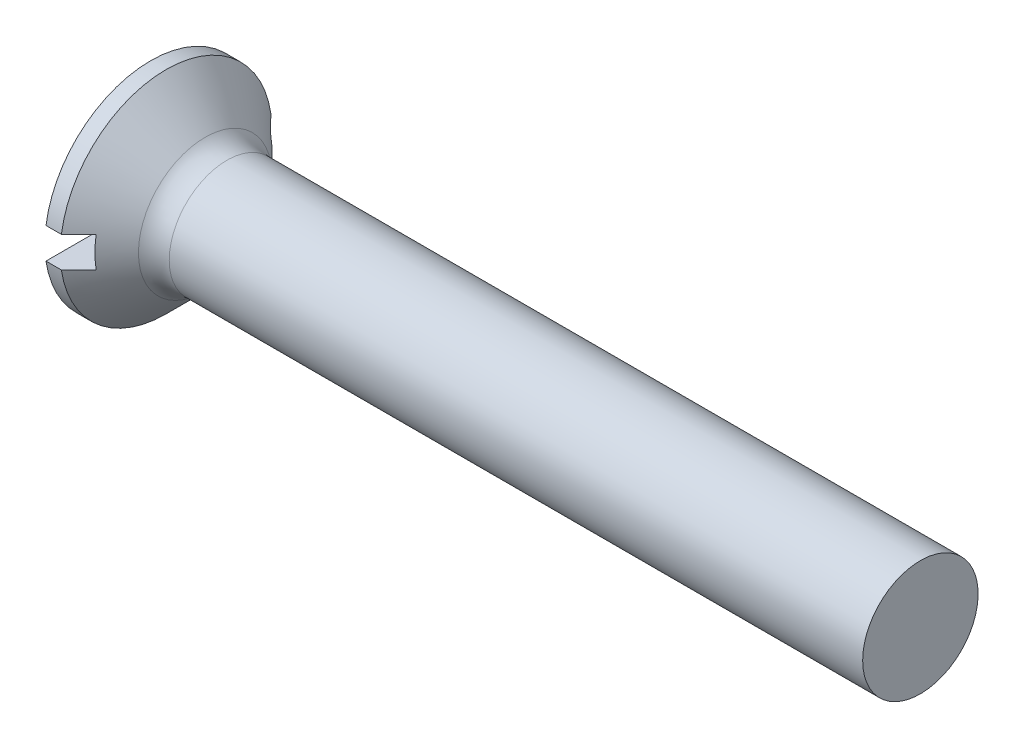
SolidWorks part; units mm, degrees
revolve "Base-Revolve" add sketch "BodySke" angle 360 about L5
sketch "BodySke" plane through (0, 0, 0) normal (0, 0, 1) x (1, 0, 0)
  line L0 (0, 0) -> (0, 2.75)
  line L1 (0, 2.75) -> (0.4, 2.75)
  line L2 (1.65, 1.5) -> (20, 1.5)
  line L3 (20, 1.5) -> (20, 0)
  line L4 (20, 0) -> (0, 0)
  line L5 (-6.35, 0) -> (82.55, 0) construction
  line L6 (1.65, -1.5) -> (20, -1.5) construction
  line L7 (0.4, -2.75) -> (1.65, -1.5) construction
  line L8 (0.4, 2.75) -> (1.65, 1.5)
  line L9 (0, -2.75) -> (0.4, -2.75) construction
  line L10 (2.15, 3.0875) -> (2.15, -6.4375) construction
  line L11 (0, 6.35) -> (0, -3.175) construction
  dimension "Diameter" = 3
  dimension "Length" = 20
  dimension "Head_ht" = 1.65
  dimension "Head_dia" = 5.5
  dimension "Head_ang" = 90
  dimension "D6" = 0.4
  dimension "Advance" = 0.5
  dimension "Thread_nom" = 20
cosmetic thread "ThreadCosmetic" [suppressed] parameters "Thread_length"=17.85, "Thread_minor"=2.439
extrude "Slot" cut sketch "Sketch2" against normal blind 0.85
sketch "Sketch2" plane through (0, 0, 0) normal (-1, 0, 0) x (0, 0, 1)
  line L0 (-2.75, -0.4) -> (2.75, -0.4)
  line L1 (-2.75, -0.4) -> (-2.75, 0.4)
  line L2 (2.75, 0.4) -> (-2.75, 0.4)
  line L3 (2.75, 0.4) -> (2.75, -0.4)
  dimension "Slot_width" = 0.8
  dimension "D1" = 0.4
  dimension "D2" = 5.5
  dimension "D3" = 2.75
ref_plane "Plane1" through (0, 0, 0) normal (0, 0, 1) x (1, 0, 0)
ref_plane "Plane2" through (0, 0, 0) normal (0, 1, 0) x (1, 0, 0)
ref_plane "Plane3" through (0, 0, 0) normal (1, 0, 0) x (0, 0, -1)
fillet "Fillet1" radius 0.8 1 edges at (1.65, 0, 1.5)
sketch "ThdSchSke" plane through (0, 0, 0) normal (0, 0, 1) x (1, 0, 0)
  line L0 (2.15, -1.2195) -> (1.9536, -1.5)
  line L1 (2.15, -1.2195) -> (2.3464, -1.5)
  line L2 (2.3464, -1.5) -> (2.3464, -1.875)
  line L3 (-3.175, 0) -> (5.1513, 0) construction
  line L5 (2.3464, -1.875) -> (1.9536, -1.875)
  line L6 (1.9536, -1.875) -> (1.9536, -1.5)
  line L7 (0, 2.75) -> (0, 0.4) construction
  dimension "Diameter" = 3
  dimension "Thread_minor" = 2.439
  dimension "Start" = 2.15
revolve "ThreadSchematic" [suppressed] cut sketch "ThdSchSke" angle 360 about L3
pattern_linear "ThdSchPat" [suppressed]
equation "\"D1@Sketch2\" = \"Slot_width@Sketch2\" / 2"
equation "\"D2@Sketch2\" = \"Head_dia@BodySke\""
equation "\"D3@Sketch2\" = \"D2@Sketch2\" / 2"
equation "\"Thread_length@ThreadCosmetic\" = ((sgn( (\"Length@BodySke\" - \"Advance@BodySke\" * 1.0 - \"Head_ht@BodySke\" ) - \"Thread_nom@BodySke\" )-1)*( (\"Length@BodySke\" - \"Advance@BodySke\" * 1.0 - \"Head_ht@BodySke\" ) - \"Thread_nom@BodySke\" ))/-2+ \"Thread_nom@BodySke\""
equation "\"Thread_minor@ThdSchSke\" = \"Thread_minor@ThreadCosmetic\""
equation "\"Diameter@ThdSchSke\" = \"Diameter@BodySke\""
equation "\"Overcut@ThdSchSke\" = \"Diameter@BodySke\" * 1.25"
equation "\"Start@ThdSchSke\" = 0.000001 + \"Length@BodySke\" - \"Thread_length@ThreadCosmetic\"  '---Countersunk---"
equation "\"Num_threads@ThdSchPat\" = int( \"Thread_length@ThreadCosmetic\" / \"Advance@BodySke\" + 0.999 )  + 1"
equation "\"Advance@ThdSchPat\" = \"Thread_length@ThreadCosmetic\" /  (\"Num_threads@ThdSchPat\" - 1) 'relax it"
